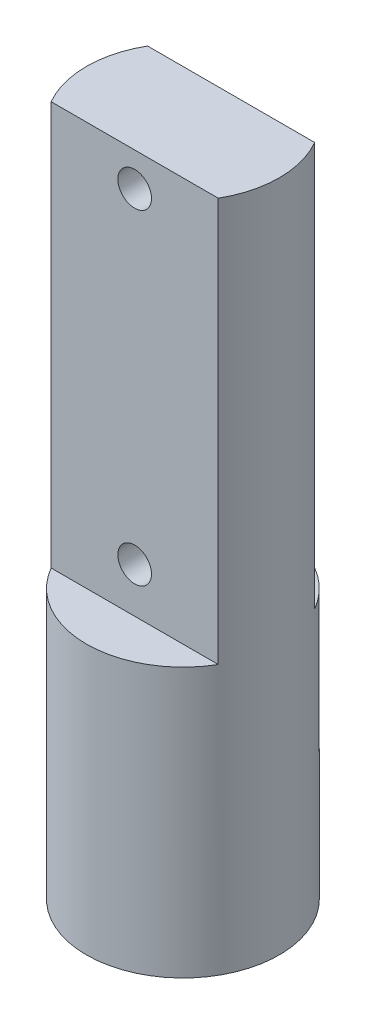
SolidWorks part; units mm, degrees
ref_plane "Front Plane" through (0, 0, 0) normal (0, 0, 1) x (1, 0, 0)
ref_plane "Top Plane" through (0, 0, 0) normal (0, 1, 0) x (1, 0, 0)
ref_plane "Right Plane" through (0, 0, 0) normal (1, 0, 0) x (0, 0, -1)
sketch "Sketch1" plane through (0, 0, 0) normal (0, 1, 0) x (1, 0, 0)
  line L0 (-4.3, 4.3) -> (4.3, 4.3)
  line L1 (-4.5, -4.5) -> (4.5, -4.5) construction
  line L2 (-4.5, -4.5) -> (-4.5, 4.5) construction
  line L3 (-4.5, 4.5) -> (4.5, 4.5) construction
  line L4 (4.5, -4.5) -> (4.5, 4.5) construction
  line L5 (4.3, -4.3) -> (4.3, 4.3)
  line L6 (-4.3, -4.3) -> (4.3, -4.3)
  line L7 (-4.3, -4.3) -> (-4.3, 4.3)
  point P0 (0, 0)
  dimension "D1" = 9
  dimension "D2" = 9
  dimension "D3" = 0.2
sketch "Sketch2" plane through (0, 0, 0) normal (0, 1, 0) x (1, 0, 0)
  circle A0 centre (0, 0) radius 4.3
extrude "Boss-Extrude2" add sketch "Sketch2" along normal blind 30
sketch "Sketch4" plane through (0, 30, 0) normal (0, 1, 0) x (1, 0, 0)
  line L0 (0, 4.3) -> (0, 0) construction
  line L1 (-4.3, 0) -> (4.3, 0) construction
  line L2 (0, 2.15) -> (-3.7239, 2.15)
  line L3 (0, 2.15) -> (3.7239, 2.15)
  line L4 (0, -2.15) -> (-3.7239, -2.15)
  line L5 (0, -2.15) -> (3.7239, -2.15)
  circle A1 centre (0, 0) radius 4.3 construction
  arc A2 (-3.7239, 2.15) -> (3.7239, 2.15) centre (0, 0) cw
  arc A3 (-3.7239, -2.15) -> (3.7239, -2.15) centre (0, 0) ccw
extrude "Cut-Extrude2" cut sketch "Sketch4" against normal blind 18
sketch "Sketch5" plane through (0, 30, 0) normal (0, 1, 0) x (1, 0, 0)
  line L2 (-3.7239, -2.15) -> (3.7239, -2.15)
  line L3 (3.7239, 2.15) -> (-3.7239, 2.15)
  line L4 (-3.7239, -2.15) -> (3.7239, -2.15)
  line L5 (3.7239, 2.15) -> (-3.7239, 2.15)
  arc A2 (3.7239, -2.15) -> (3.7239, 2.15) centre (0, 0) ccw
  arc A3 (-3.7239, 2.15) -> (-3.7239, -2.15) centre (0, 0) ccw
  arc A4 (3.7239, -2.15) -> (3.7239, 2.15) centre (0, 0) ccw
  arc A5 (-3.7239, 2.15) -> (-3.7239, -2.15) centre (0, 0) ccw
  dimension "D1" = 0
sketch "Sketch6" plane through (0, 0, 2.15) normal (0, 0, 1) x (1, 0, 0)
  line L0 (0, 12) -> (0, 12.5) construction
  line L1 (3.7239, 12) -> (-3.7239, 12) construction
  line L2 (0, 12.5) -> (-4.3, 12.5) construction
  line L3 (-4.3, 30) -> (-4.3, 0) construction
  line L4 (-4.3, 12.5) -> (-4.3, 15.5) construction
  line L5 (-4.3, 15.5) -> (4.3, 15.5) construction
  line L6 (4.3, 0) -> (4.3, 30) construction
  line L7 (4.3, 15.5) -> (4.3, 12.5) construction
  line L8 (4.3, 12.5) -> (0, 12.5) construction
  line L9 (0, 15.5) -> (0, 12.5) construction
  circle A0 centre (0, 14) radius 0.75
  dimension "D2" = 1.5
  dimension "D1" = 0.5
  dimension "D3" = 3
extrude "Cut-Extrude3" cut sketch "Sketch6" against normal blind 10
sketch "Sketch8" plane through (0, 0, 0) normal (1, 0, 0) x (0, 0, -1)
  line L0 (0, 5) -> (0, 2) construction
  line L1 (0, 2) -> (0, 0) construction
  circle A0 centre (0, 1) radius 0.75
  dimension "D2" = 1.5
  dimension "D1" = 3
extrude "Cut-Extrude5" cut sketch "Sketch8" against normal through all
sketch "Sketch9" plane through (0, 0, 2.15) normal (0, 0, 1) x (1, 0, 0)
  line L0 (0, 30) -> (0, 28.5) construction
  line L1 (-3.7239, 30) -> (3.7239, 30) construction
  circle A0 centre (0, 28.5) radius 0.75
  dimension "D1" = 1.5
extrude "Cut-Extrude6" cut sketch "Sketch9" against normal blind 10
